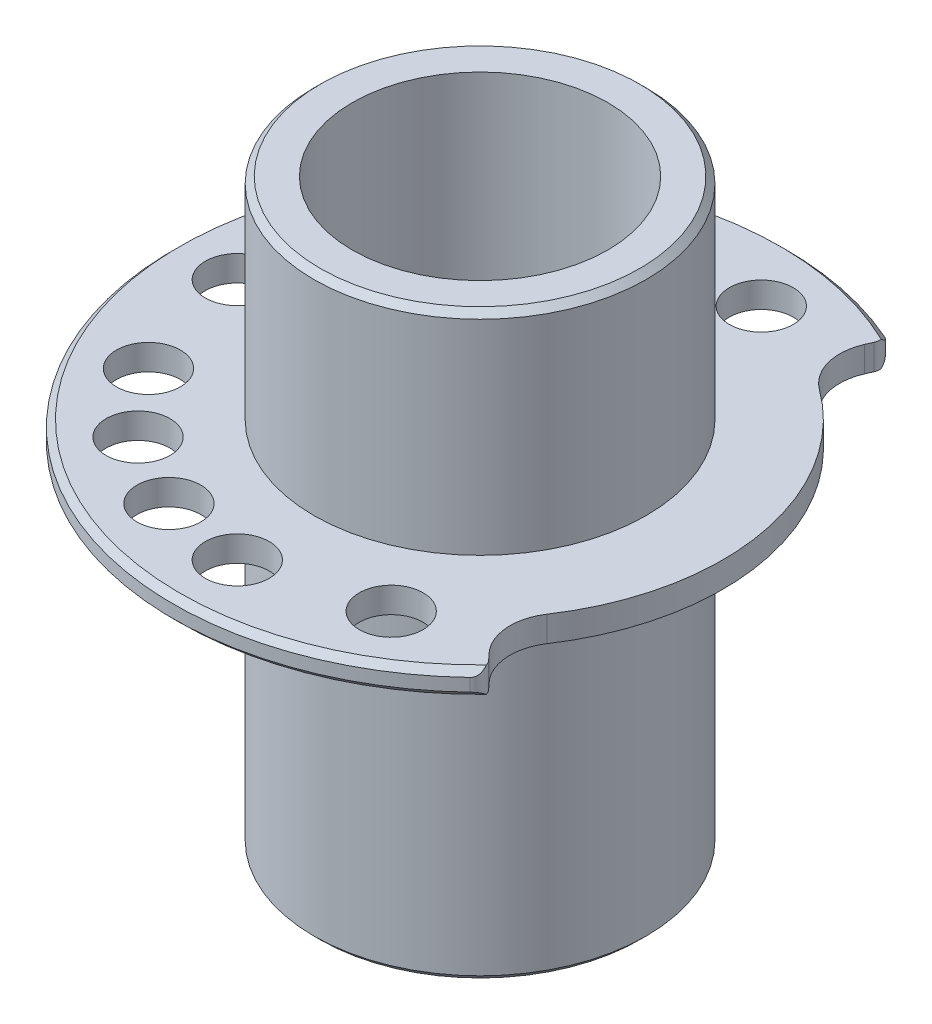
SolidWorks part; units mm, degrees
material "1.7218 (25CrMo4)"
ref_plane "Płaszczyzna XY" through (0, 0, 0) normal (0, 0, 1) x (1, 0, 0)
ref_plane "Płaszczyzna XZ" through (0, 0, 0) normal (0, 1, 0) x (1, 0, 0)
ref_plane "Płaszczyzna YZ" through (0, 0, 0) normal (1, 0, 0) x (0, 0, -1)
sketch "Sketch1" plane through (0, 0, 0) normal (0, 1, 0) x (1, 0, 0)
  circle A0 centre (0, 0) radius 13
  dimension "D1" = 26
extrude "Boss-Extrude1" add sketch "Sketch1" against normal blind 28
sketch "Sketch3" plane through (0, 0, 0) normal (0, 1, 0) x (1, 0, 0)
  circle A0 centre (0, 0) radius 24
  dimension "D1" = 48
extrude "Boss-Extrude2" add sketch "Sketch3" along normal mid plane 2 contours A0
sketch "Sketch2" plane through (0, -28, 0) normal (0, -1, 0) x (-1, 0, 0)
  circle A0 centre (0, 0) radius 10
  dimension "D1" = 20
extrude "Cut-Extrude1" cut sketch "Sketch2" against normal through all both and the other way through all
sketch "Sketch7" plane through (0, -1, 0) normal (0, -1, 0) x (1, 0, 0)
  line L0 (0, 0) -> (-36.0692, 0) construction
  line L1 (0, 0) -> (0, 31.096) construction
  line L2 (0, 0) -> (4.2228, -23.9489) construction
  line L3 (0, 0) -> (-9.7059, 26.6668) construction
  line L4 (0, 0) -> (19.241, 33.3264) construction
  line L5 (0, 0) -> (-13.1468, -28.1934) construction
  line L6 (0, 0) -> (-33.8658, 40.3597) construction
  line L7 (0, 0) -> (-26.1602, -21.951) construction
  line L8 (0, 0) -> (-48.4112, 27.9502) construction
  circle A13 centre (0, 0) radius 19 construction
  circle A15 centre (0, 19) radius 2.5
  circle A16 centre (3.2993, -18.7113) radius 2.5
  circle A18 centre (-6.4979, 17.8529) radius 2.5
  circle A19 centre (9.5, 16.4545) radius 2.5
  circle A21 centre (-19, 0) radius 2.5
  circle A22 centre (-8.0297, -17.2198) radius 2.5
  circle A23 centre (-12.213, 14.5548) radius 2.5
  circle A24 centre (-14.5754, -12.2302) radius 2.5
  circle A25 centre (-16.4545, 9.5) radius 2.5
  dimension "D1" = 38
  dimension "D6" = 20
  dimension "D7" = 30
  dimension "D9" = 5
  dimension "D10" = 155
  dimension "D12" = 40
  dimension "D13" = 5
  dimension "D14" = 130
  dimension "D16" = 5
  dimension "D8" = 5
  dimension "D2" = 5
  dimension "D4" = 5
  dimension "D5" = 5
  dimension "D11" = 5
  dimension "D15" = 5
  dimension "D3" = 170
  dimension "D17" = 60
sketch "Sketch9" plane through (0, 0, 0) normal (0, 1, 0) x (1, 0, 0)
  circle A0 centre (0, 0) radius 13
  dimension "D1" = 26
extrude "Boss-Extrude3" add sketch "Sketch9" along normal blind 17.5
chamfer "Chamfer2" distance 0.5 angle 45 1 edges at (0, -1, 24)
chamfer "Chamfer3" distance 0.5 angle 45 1 edges at (0, 1, 24)
chamfer "Chamfer4" distance 0.5 angle 45 1 edges at (0, -28, 13)
sketch "Sketch11" plane through (0, 17.5, 0) normal (0, 1, 0) x (1, 0, 0)
  circle A0 centre (0, 0) radius 10
  dimension "D1" = 20
extrude "Cut-Extrude5" cut sketch "Sketch11" against normal through all both and the other way through all
chamfer "Chamfer5" distance 0.5 angle 45 1 edges at (0, 17.5, 13)
extrude "Wytnij-wyciągnięcie1" cut sketch "Sketch7" against normal through all both and the other way through all
sketch "Szkic1" plane through (0, 1, 0) normal (0, 1, 0) x (1, 0, 0)
  line L0 (13.8316, -13.0264) -> (17.2898, -16.6452)
  line L1 (8.5422, 16.9715) -> (10.5541, 21.5548)
  arc A0 (17.2898, -16.6452) -> (10.5541, 21.5548) centre (0, 0) ccw
  arc A1 (13.8316, -13.0264) -> (8.5422, 16.9715) centre (0, 0) ccw
  circle A2 centre (3.2993, 18.7113) radius 2.5 construction
  circle A3 centre (9.5, -16.4545) radius 2.5 construction
  dimension "D1" = 38
  dimension "D2" = 5.5
  dimension "D3" = 5.5
extrude "Wytnij-wyciągnięcie2" cut sketch "Szkic1" against normal blind 10
fillet "Zaokrąglenie1" radius 4 2 edges at (13.8316, 0, 13.0264) (8.5422, 0, -16.9715)
fillet "Zaokrąglenie2" radius 1 2 edges at (10.5541, 0, -21.5548) (17.2898, 0, 16.6452)
